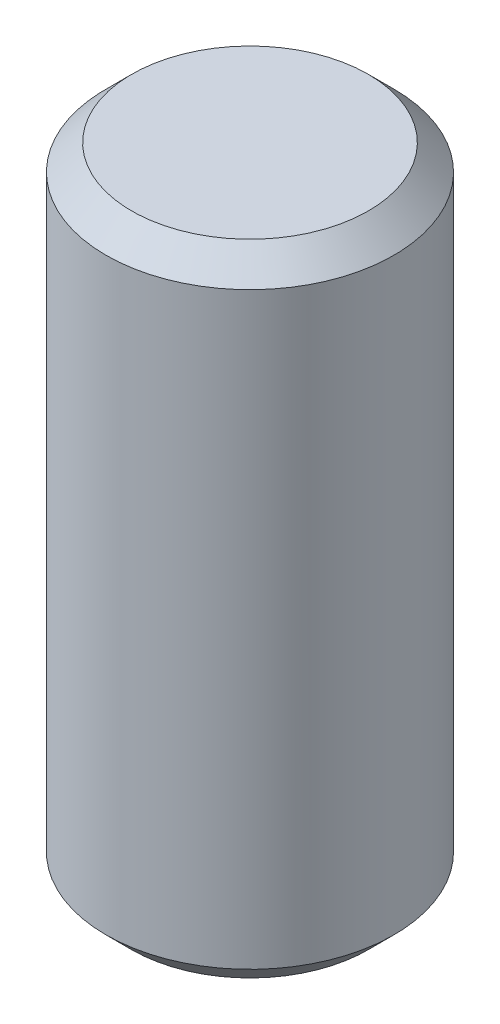
SolidWorks part; units mm, degrees
ref_plane "Front" through (0, 0, 0) normal (0, 0, 1) x (1, 0, 0)
ref_plane "Top" through (0, 0, 0) normal (0, 1, 0) x (1, 0, 0)
ref_plane "Right" through (0, 0, 0) normal (1, 0, 0) x (0, 0, -1)
sketch "Sketch1" plane through (0, 0, 0) normal (0, 0, 1) x (1, 0, 0)
  line L0 (0, 6.0802) -> (0, -6.0802) construction
  line L1 (0, -6.35) -> (2.8575, -6.35)
  line L2 (2.8575, -6.35) -> (2.8575, 6.35)
  line L3 (2.8575, 6.35) -> (0, 6.35)
  line L4 (0, 6.35) -> (0, -6.35)
  point P6 (0, 0)
  dimension "D1" = 5.715
  dimension "D2" = 12.7
revolve "Revolve1" add sketch "Sketch1" angle 360 about L0
chamfer "Chamfer1" distance 0.508 angle 45 2 edges at (0, -6.35, 2.8575) (0, 6.35, 2.8575)
